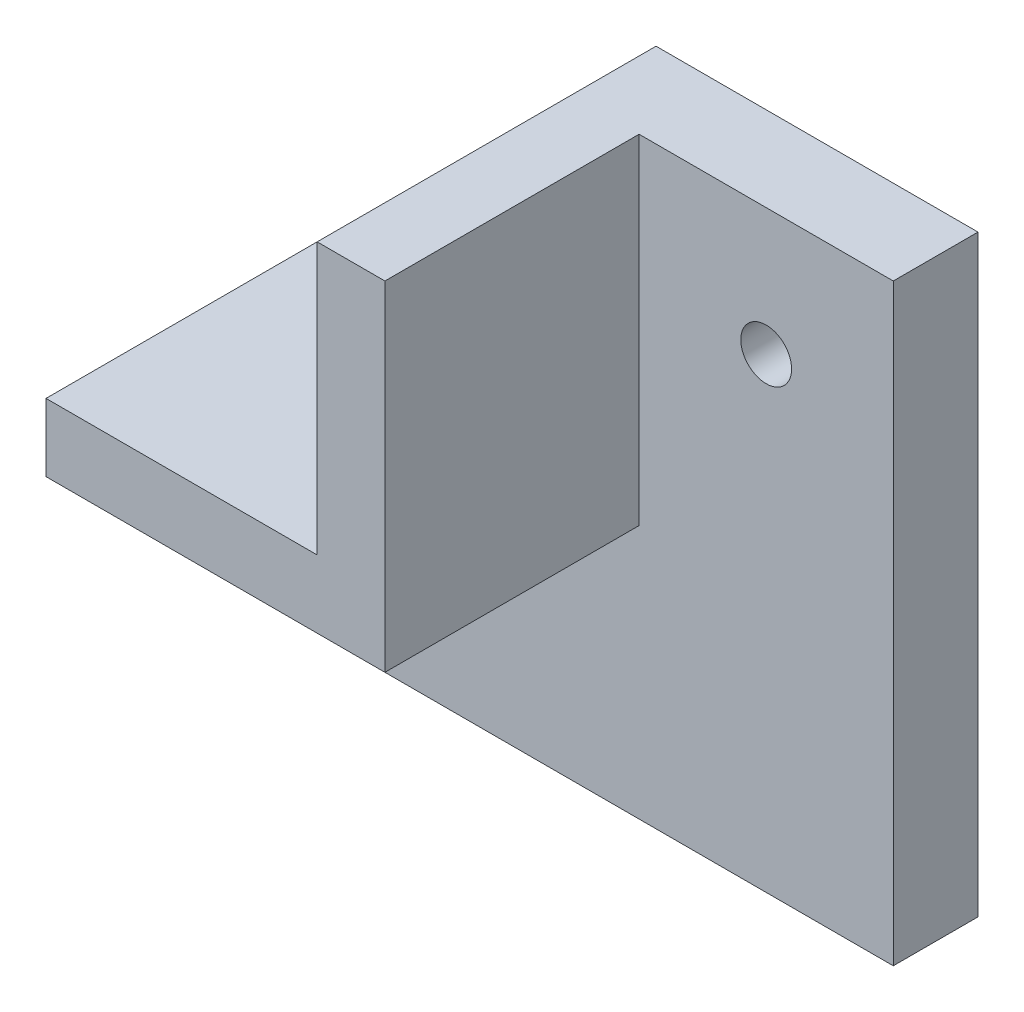
SolidWorks part; units mm, degrees
ref_plane "Front Plane" through (0, 0, 0) normal (0, 0, 1) x (1, 0, 0)
ref_plane "Top Plane" through (0, 0, 0) normal (0, 1, 0) x (1, 0, 0)
ref_plane "Right Plane" through (0, 0, 0) normal (1, 0, 0) x (0, 0, -1)
sketch "Sketch1" plane through (0, 0, 0) normal (0, 0, 1) x (1, 0, 0)
  line L0 (14.3137, -4.2647) -> (34.3137, -4.2647)
  line L1 (-20.6863, -4.2647) -> (-0.6863, -4.2647)
  line L2 (-20.6863, -4.2647) -> (-20.6863, -19.2647)
  line L3 (-20.6863, -19.2647) -> (34.3137, -19.2647)
  line L4 (34.3137, -4.2647) -> (34.3137, -19.2647)
  line L5 (-0.6863, 15.7353) -> (14.3137, 15.7353)
  line L6 (-0.6863, 15.7353) -> (-0.6863, -4.2647)
  line L8 (14.3137, 15.7353) -> (14.3137, -4.2647)
  dimension "D1" = 15
  dimension "D2" = 20
  dimension "D3" = 20
  dimension "D4" = 15
  dimension "D5" = 20
extrude "Boss-Extrude1" add sketch "Sketch1" along normal blind 5
sketch "Sketch2" plane through (0, 0, 0) normal (0, 0, -1) x (-1, 0, 0)
  line L0 (0.6863, 15.7353) -> (4.6863, 15.7353)
  line L1 (4.6863, 15.7353) -> (4.6863, -0.2647)
  line L2 (20.6863, -4.2647) -> (20.6863, -0.2647)
  line L3 (20.6863, -0.2647) -> (6.08, -0.2647)
  line L4 (20.6863, -4.2647) -> (0.6863, -4.2647)
  line L5 (0.6863, 15.7353) -> (0.6863, -4.2647)
  line L6 (6.08, -0.2647) -> (4.6863, -0.2647)
  dimension "D1" = 4
  dimension "D2" = 4
extrude "Boss-Extrude2" add sketch "Sketch2" against normal blind 20 contours L3 L6 L1 L0 L5 L4 L2
ref_plane "Plane4" through (6.8137, 0, 0) normal (-1, 0, 0) x (0, 0, 1)
ref_plane "Plane5" through (-5.6863, 0, 0) normal (-1, 0, 0) x (0, 0, 1)
ref_plane "Plane6" through (-4.6863, -0.2647, 20) normal (0, -1, 0) x (-1, 0, 0)
sketch "Sketch3" plane through (0, 0, 0) normal (0, 0, -1) x (-1, 0, 0)
  line L1 (-14.3137, -4.2647) -> (-34.3137, -4.2647)
  line L2 (-14.3137, -4.2647) -> (-14.3137, -19.2647)
  line L3 (-14.3137, -19.2647) -> (-34.3137, -19.2647)
  line L4 (-34.3137, -4.2647) -> (-34.3137, -19.2647)
extrude "Cut-Extrude1" cut sketch "Sketch3" against normal through all
sketch "Sketch4" plane through (0, 0, 0) normal (0, 0, -1) x (-1, 0, 0)
  line L0 (-14.3137, 15.7353) -> (4.6863, 15.7353) construction
  line L1 (20.6863, -0.2647) -> (20.6863, -19.2647) construction
  line L2 (20.6863, -19.2647) -> (-14.3137, -19.2647) construction
  line L3 (-14.3137, -19.2647) -> (-14.3137, 15.7353) construction
  circle A0 centre (-6.8137, 8.2353) radius 1.5
  circle A1 centre (13.1863, -11.7647) radius 1.5
  dimension "D1" = 3
  dimension "D2" = 3
  dimension "D3" = 7.5
  dimension "D4" = 7.5
  dimension "D5" = 7.5
  dimension "D6" = 7.5
extrude "Cut-Extrude2" cut sketch "Sketch4" against normal through all
